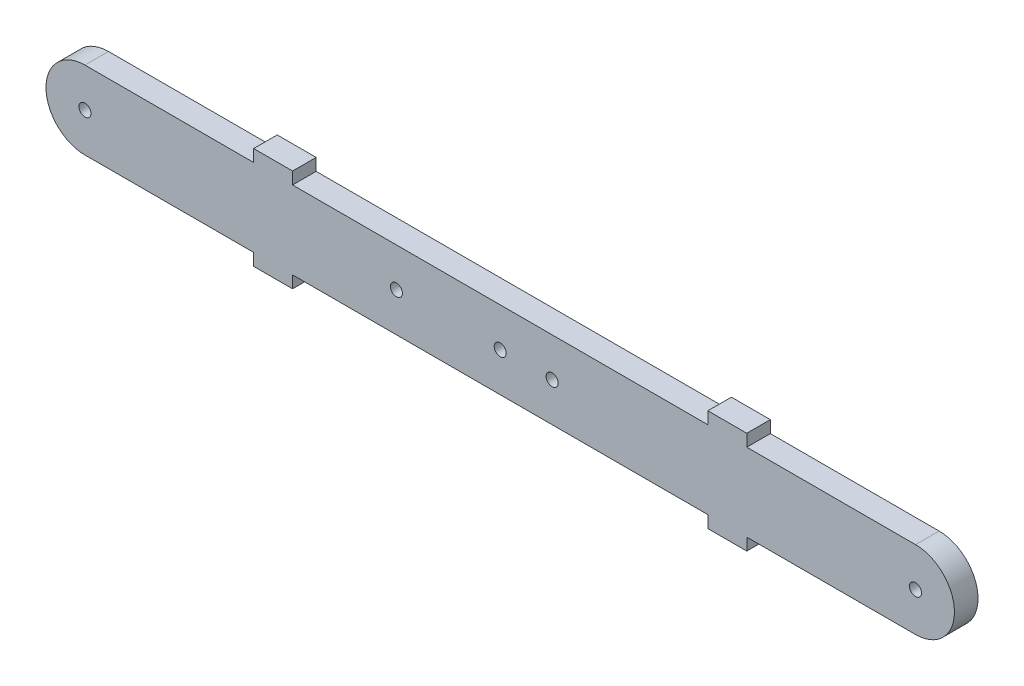
SolidWorks part; units mm, degrees
ref_plane "Front Plane" through (0, 0, 0) normal (0, 0, 1) x (1, 0, 0)
ref_plane "Top Plane" through (0, 0, 0) normal (0, 1, 0) x (1, 0, 0)
ref_plane "Right Plane" through (0, 0, 0) normal (1, 0, 0) x (0, 0, -1)
sketch "Sketch1" plane through (0, 0, 0) normal (0, 0, 1) x (1, 0, 0)
  line L0 (-101.6, 0) -> (101.6, 0) construction
  line L1 (-101.6, 9.525) -> (101.6, 9.525)
  line L2 (-101.6, -9.525) -> (101.6, -9.525)
  arc A0 (-101.6, 9.525) -> (-101.6, -9.525) centre (-101.6, 0) ccw
  arc A1 (101.6, -9.525) -> (101.6, 9.525) centre (101.6, 0) ccw
  circle A2 centre (-101.6, 0) radius 1.4732
  circle A3 centre (101.6, 0) radius 1.4732
  point P3 (0, 0)
  dimension "D2" = 2.9464
  dimension "D3" = 19.05
  dimension "D1" = 203.2
extrude "Boss-Extrude1" add sketch "Sketch1" along normal blind 5.7658
hole_wizard "#4 Clearance Hole1" positions "Sketch4" profile "Sketch3" hole size "#4" standard "ANSI Inch" end condition through all
sketch "Sketch4" plane through (0, 0, 5.7658) normal (0, 0, 1) x (1, 0, 0)
  line L0 (-101.6, 0) -> (101.6, 0) construction
  line L1 (0, 16.6936) -> (0, -19.7024) construction
  point P18 (-25.4, 0)
  point P31 (12.7, 0)
  point P32 (0, 0)
  dimension "D1" = 76.2
  dimension "D2" = 114.3
sketch "Sketch3" plane through (-25.4, 0, 5.7658) normal (1, 0, 0) x (0, -1, 0)
  line L0 (0, 0) -> (0, 5.7658)
  line L1 (0, 5.7658) -> (1.4732, 5.7658)
  line L2 (1.4732, 5.7658) -> (1.4732, 0)
  line L5 (1.4732, 0) -> (0, 0)
  line L11 (0, -6.35) -> (0, 107.95) construction
  dimension "Thru Hole Dia." = 2.9464
  dimension "Thru Hole Depth" = 5.7658
sketch "Sketch5" plane through (0, 0, 5.7658) normal (0, 0, 1) x (1, 0, 0)
  line L0 (101.6, 9.525) -> (-101.6, 9.525) construction
  line L1 (60.325, 9.525) -> (50.8, 9.525)
  line L2 (60.325, 9.525) -> (60.325, 12.4841)
  line L3 (60.325, 12.4841) -> (50.8, 12.4841)
  line L4 (50.8, 9.525) -> (50.8, 12.4841)
  line L5 (0, 7.386) -> (0, -7.7985) construction
  line L6 (4.0167, 0) -> (-4.6145, 0) construction
  line L7 (-50.8, 9.525) -> (-50.8, 12.4841)
  line L8 (-60.325, 12.4841) -> (-50.8, 12.4841)
  line L9 (-60.325, 9.525) -> (-60.325, 12.4841)
  line L10 (-60.325, 9.525) -> (-50.8, 9.525)
  line L11 (-60.325, -9.525) -> (-50.8, -9.525)
  line L12 (-60.325, -9.525) -> (-60.325, -12.4841)
  line L13 (-60.325, -12.4841) -> (-50.8, -12.4841)
  line L14 (-50.8, -9.525) -> (-50.8, -12.4841)
  line L15 (50.8, -9.525) -> (50.8, -12.4841)
  line L16 (60.325, -12.4841) -> (50.8, -12.4841)
  line L17 (60.325, -9.525) -> (60.325, -12.4841)
  line L18 (60.325, -9.525) -> (50.8, -9.525)
  point P9 (12.7, 0)
  dimension "D1" = 9.525
  dimension "D2" = 2.9591
  dimension "D3" = 101.6
extrude "Boss-Extrude2" add sketch "Sketch5" against normal up to surface (5.7658 mm away) up to face at (-23.9268, 0, 0)
